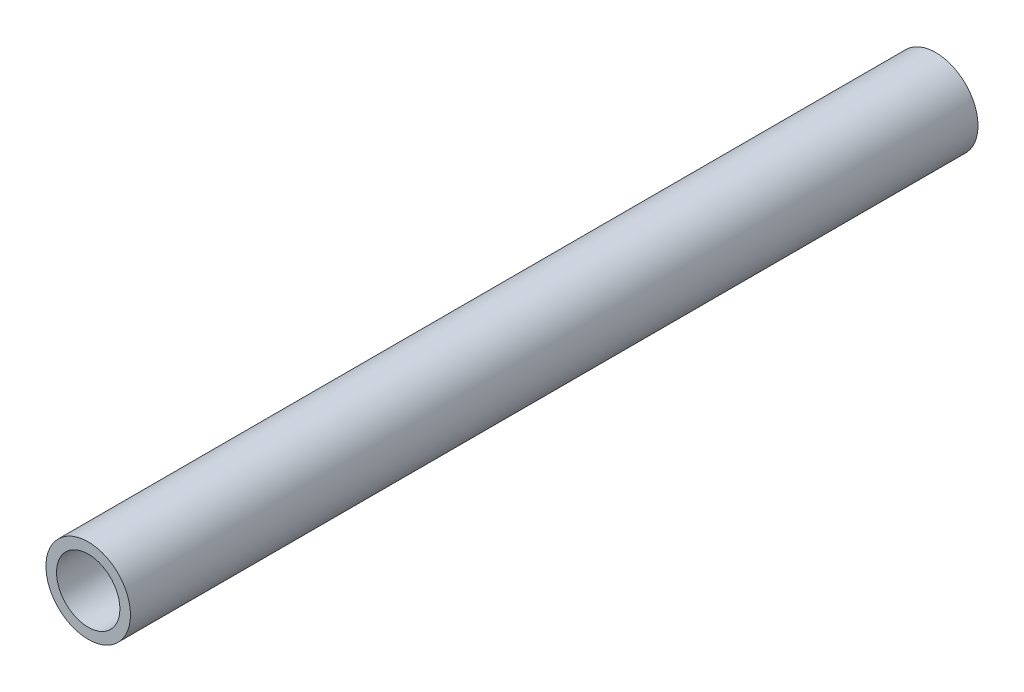
SolidWorks part; units mm, degrees
material "Copper"
ref_plane "Front Plane" through (0, 0, 0) normal (0, 0, 1) x (1, 0, 0)
ref_plane "Top Plane" through (0, 0, 0) normal (0, 1, 0) x (1, 0, 0)
ref_plane "Right Plane" through (0, 0, 0) normal (1, 0, 0) x (0, 0, -1)
sketch "Sketch2" plane through (0, 0, 0) normal (0, 0, 1) x (1, 0, 0)
  circle A0 centre (0, 0) radius 50.8
  dimension "D1" = 101.6
extrude "Extrude-Thin1" add sketch "Sketch2" along normal blind 1018.54 thin thin type one direction reverse wall 12.7
